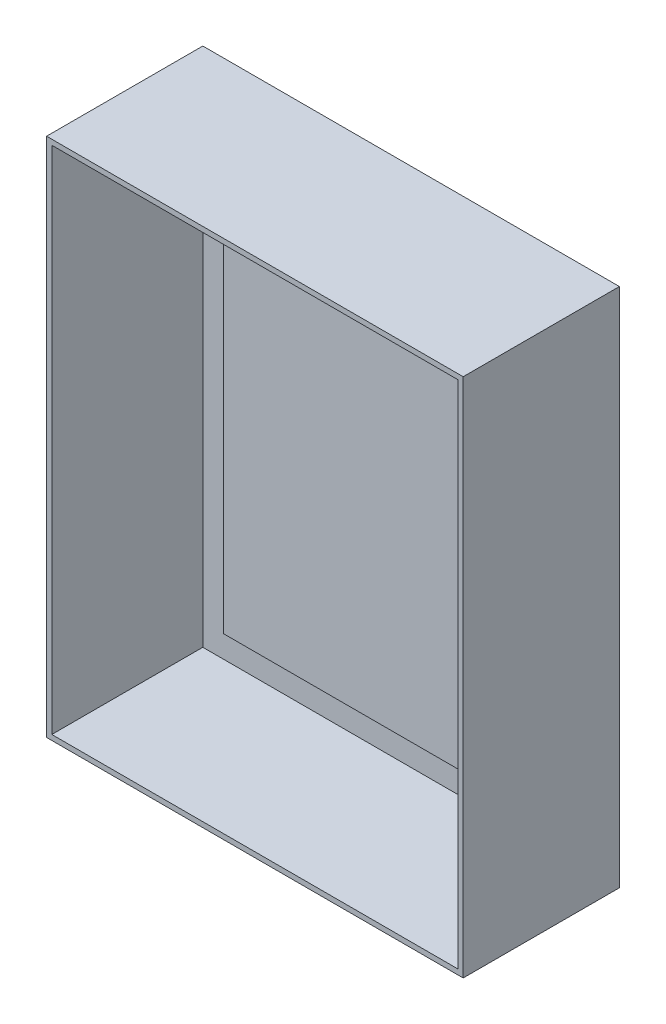
SolidWorks part; units mm, degrees
ref_plane "Front Plane" through (0, 0, 0) normal (0, 0, 1) x (1, 0, 0)
ref_plane "Top Plane" through (0, 0, 0) normal (0, 1, 0) x (1, 0, 0)
ref_plane "Right Plane" through (0, 0, 0) normal (1, 0, 0) x (0, 0, -1)
sketch "Sketch1" plane through (0, 0, 0) normal (0, 0, 1) x (1, 0, 0)
  line L1 (-203.2, 254) -> (203.2, 254)
  line L2 (-203.2, 254) -> (-203.2, -254)
  line L3 (-203.2, -254) -> (203.2, -254)
  line L4 (203.2, 254) -> (203.2, -254)
  line L5 (-203.2, 254) -> (203.2, -254) construction
  line L6 (-203.2, -254) -> (203.2, 254) construction
  point P0 (0, 0)
  dimension "D1" = 406.4
  dimension "D2" = 508
extrude "Boss-Extrude1" add sketch "Sketch1" along normal blind 152.4
shell "Shell1" thickness 5.08
sketch "Sketch2" plane through (0, 0, 5.08) normal (0, 0, 1) x (1, 0, 0)
  line L1 (-175.26, 224.79) -> (175.26, 224.79)
  line L2 (-175.26, 224.79) -> (-175.26, -224.79)
  line L3 (-175.26, -224.79) -> (175.26, -224.79)
  line L4 (175.26, 224.79) -> (175.26, -224.79)
  line L5 (-175.26, 224.79) -> (175.26, -224.79) construction
  line L6 (-175.26, -224.79) -> (175.26, 224.79) construction
  point P0 (0, 0)
  dimension "D1" = 350.52
  dimension "D2" = 449.58
extrude "Boss-Extrude2" add sketch "Sketch2" along normal blind 2.54
